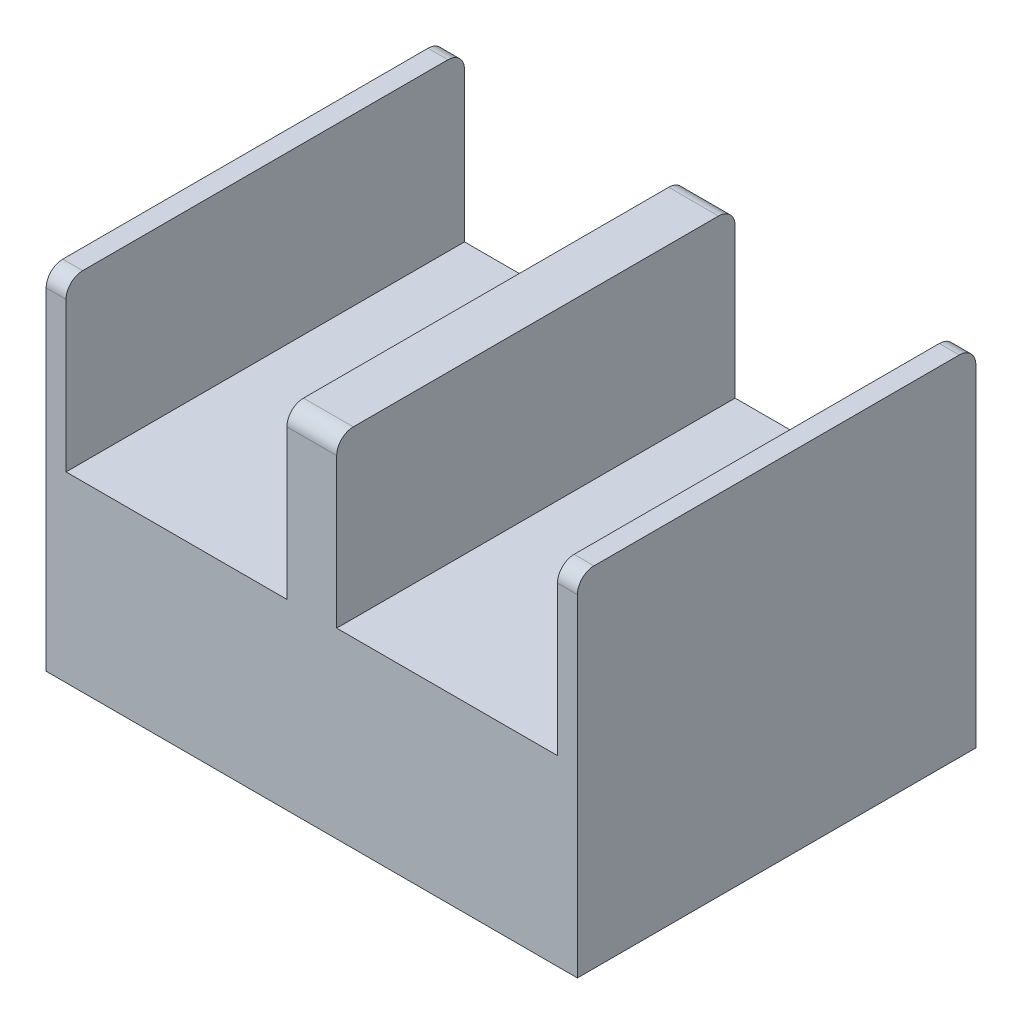
SolidWorks part; units mm, degrees
ref_plane "Front Plane" through (0, 0, 0) normal (0, 0, 1) x (1, 0, 0)
ref_plane "Top Plane" through (0, 0, 0) normal (0, 1, 0) x (1, 0, 0)
ref_plane "Right Plane" through (0, 0, 0) normal (1, 0, 0) x (0, 0, -1)
sketch "Sketch1" plane through (0, 0, 0) normal (0, 1, 0) x (1, 0, 0)
  line L1 (-8, -6) -> (8, -6)
  line L2 (-8, -6) -> (-8, 6)
  line L3 (-8, 6) -> (8, 6)
  line L4 (8, -6) -> (8, 6)
  line L5 (-8, -6) -> (8, 6) construction
  line L6 (-8, 6) -> (8, -6) construction
  point P0 (0, 0)
  dimension "D1" = 16
  dimension "D2" = 12
extrude "Boss-Extrude1" add sketch "Sketch1" along normal blind 5.5
sketch "Sketch2" plane through (0, 5.5, 0) normal (0, 1, 0) x (1, 0, 0)
  line L0 (-8, -6) -> (8, -6) construction
  line L1 (-8, 6) -> (-7.4, 6)
  line L2 (-8, 6) -> (-8, -6)
  line L3 (-8, -6) -> (-7.4, -6)
  line L4 (-7.4, 6) -> (-7.4, -6)
  line L5 (8, 6) -> (-8, 6) construction
  line L6 (8, -6) -> (7.4, -6)
  line L7 (8, -6) -> (8, 6)
  line L8 (8, 6) -> (7.4, 6)
  line L9 (7.4, -6) -> (7.4, 6)
  line L11 (-0.75, 6) -> (0.75, 6)
  line L12 (-0.75, 6) -> (-0.75, -6)
  line L13 (-0.75, -6) -> (0.75, -6)
  line L14 (0.75, 6) -> (0.75, -6)
  point P18 (0, 6)
  dimension "D1" = 0.6
  dimension "D2" = 1.5
extrude "Boss-Extrude2" add sketch "Sketch2" along normal blind 5
fillet "Fillet1" radius 0.5 6 edges at (-7.7, 10.5, -6) (0, 10.5, -6) (7.7, 10.5, -6) (7.7, 10.5, 6) (0, 10.5, 6) (-7.7, 10.5, 6)
sketch "Sketch4" plane through (0, 5.5, 0) normal (0, 1, 0) x (1, 0, 0)
  line L0 (-4.075, 6) -> (-4.075, -6) construction
  line L1 (-0.75, 6) -> (-7.4, 6) construction
  line L2 (-7.4, -6) -> (-0.75, -6) construction
  line L3 (4.075, 6) -> (4.075, -6) construction
  line L4 (7.4, 6) -> (0.75, 6) construction
  line L5 (0.75, -6) -> (7.4, -6) construction
hole_wizard "M3 Tapped Hole1" positions "Sketch5" profile "Sketch6" tap size "M3" standard "ISO"
sketch "Sketch5" plane through (0, 5.5, 0) normal (0, 1, 0) x (1, 0, 0)
  line L0 (-4.075, 6) -> (-4.075, -6) construction
  line L1 (4.075, 6) -> (4.075, -6) construction
  point P0 (-4.075, 0)
  point P4 (4.075, 0)
sketch "Sketch6" plane through (-4.075, 5.5, 0) normal (1, 0, 0) x (0, 0, 1)
  line L0 (0, 0) -> (0, 10.7511)
  line L1 (0, 10.7511) -> (1.25, 10)
  line L2 (1.25, 10) -> (1.25, 0)
  line L5 (1.25, 0) -> (0, 0)
  line L10 (0, 10.7511) -> (-1.25, 10) construction
  line L11 (0, -6.35) -> (0, 107.95) construction
  dimension "Tap Drill Dia." = 2.5
  dimension "Tap Drill Depth" = 10
  dimension "Drill Angle" = 118
cosmetic thread "Hole Thread1" parameters "D1"=5.5, "D2"=3
cosmetic thread "Hole Thread2" parameters "D1"=5.5, "D2"=3
